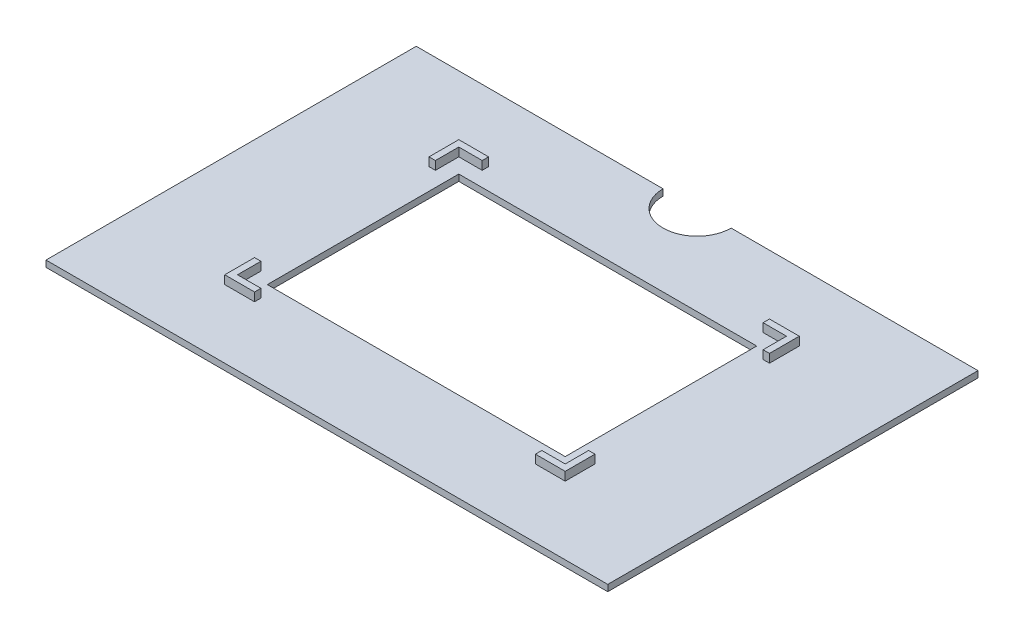
SolidWorks part; units mm, degrees
ref_plane "Front Plane" through (0, 0, 0) normal (0, 0, 1) x (1, 0, 0)
ref_plane "Top Plane" through (0, 0, 0) normal (0, 1, 0) x (1, 0, 0)
ref_plane "Right Plane" through (0, 0, 0) normal (1, 0, 0) x (0, 0, -1)
sketch "Sketch1" plane through (0, 0, 0) normal (0, 1, 0) x (1, 0, 0)
  line L1 (66, -43.5) -> (-66, -43.5)
  line L2 (66, -43.5) -> (66, 43.5)
  line L3 (66, 43.5) -> (-66, 43.5)
  line L4 (-66, -43.5) -> (-66, 43.5)
  line L5 (66, -43.5) -> (-66, 43.5) construction
  line L6 (66, 43.5) -> (-66, -43.5) construction
  point P0 (0, 0)
  dimension "D1" = 132
  dimension "D2" = 87
extrude "Boss-Extrude1" add sketch "Sketch1" along normal blind 1.5
sketch "Sketch2" plane through (0, 1.5, 0) normal (0, 1, 0) x (1, 0, 0)
  line L1 (40, -27.5) -> (-40, -27.5)
  line L2 (40, -27.5) -> (40, 27.5)
  line L3 (40, 27.5) -> (-40, 27.5)
  line L4 (-40, -27.5) -> (-40, 27.5)
  line L5 (40, -27.5) -> (-40, 27.5) construction
  line L6 (40, 27.5) -> (-40, -27.5) construction
  point P0 (0, 0)
  dimension "D1" = 80
  dimension "D2" = 55
extrude "Boss-Extrude2" add sketch "Sketch2" along normal blind 2
sketch "Sketch3" plane through (0, 3.5, 0) normal (0, 1, 0) x (1, 0, 0)
  line L1 (38.5, -26) -> (-38.5, -26)
  line L2 (38.5, -26) -> (38.5, 26)
  line L3 (38.5, 26) -> (-38.5, 26)
  line L4 (-38.5, -26) -> (-38.5, 26)
  line L5 (38.5, -26) -> (-38.5, 26) construction
  line L6 (38.5, 26) -> (-38.5, -26) construction
  point P0 (0, 0)
  dimension "D1" = 77
  dimension "D2" = 52
extrude "Cut-Extrude1" cut sketch "Sketch3" against normal blind 2
sketch "Sketch4" plane through (0, 1.5, 0) normal (0, 1, 0) x (1, 0, 0)
  line L1 (-35, 22.5) -> (35, 22.5)
  line L2 (-35, 22.5) -> (-35, -22.5)
  line L3 (-35, -22.5) -> (35, -22.5)
  line L4 (35, 22.5) -> (35, -22.5)
  line L5 (-35, 22.5) -> (35, -22.5) construction
  line L6 (-35, -22.5) -> (35, 22.5) construction
  point P0 (0, 0)
  dimension "D1" = 70
  dimension "D2" = 45
extrude "Cut-Extrude2" cut sketch "Sketch4" against normal up to next
sketch "Sketch5" plane through (0, 3.5, 0) normal (0, 1, 0) x (1, 0, 0)
  line L0 (-38.5, 26) -> (-38.5, -26) construction
  line L1 (-38.5, 20.5) -> (-40, 20.5)
  line L2 (-38.5, 20.5) -> (-38.5, -20.5)
  line L3 (-38.5, -20.5) -> (-40, -20.5)
  line L4 (-40, 20.5) -> (-40, -20.5)
  line L5 (-40, 27.5) -> (-40, -27.5) construction
  line L6 (40, 27.5) -> (-40, 27.5) construction
  line L7 (-40, -27.5) -> (40, -27.5) construction
  line L8 (0, 26) -> (0, -27.5) construction
  line L9 (38.5, 26) -> (-38.5, 26) construction
  line L10 (38.5, -20.5) -> (40, -20.5)
  line L11 (40, 20.5) -> (40, -20.5)
  line L12 (38.5, 20.5) -> (38.5, -20.5)
  line L13 (38.5, 20.5) -> (40, 20.5)
  line L14 (40, -27.5) -> (40, 27.5) construction
  line L15 (-33, 27.5) -> (33, 27.5)
  line L16 (-33, 27.5) -> (-33, 26)
  line L17 (-33, 26) -> (33, 26)
  line L18 (33, 27.5) -> (33, 26)
  line L19 (38.5, 0) -> (-38.5, 0) construction
  line L20 (33, -27.5) -> (33, -26)
  line L21 (-33, -26) -> (33, -26)
  line L22 (-33, -27.5) -> (-33, -26)
  line L23 (-33, -27.5) -> (33, -27.5)
  dimension "D1" = 7
  dimension "D2" = 7
  dimension "D3" = 7
  dimension "D4" = 7
extrude "Cut-Extrude3" cut sketch "Sketch5" against normal up to surface (2 mm away) up to face at (0, 1.5, 0)
sketch "Sketch6" plane through (0, 1.5, 0) normal (0, 1, 0) x (1, 0, 0)
  line L0 (66, 43.5) -> (-66, 43.5) construction
  line L1 (-8, 43.5) -> (8, 43.5)
  arc A0 (-8, 43.5) -> (8, 43.5) centre (0, 43.5) ccw
  dimension "D1" = 8
extrude "Cut-Extrude4" cut sketch "Sketch6" against normal up to surface (1.5 mm away) up to face at (0, 0, 0)
